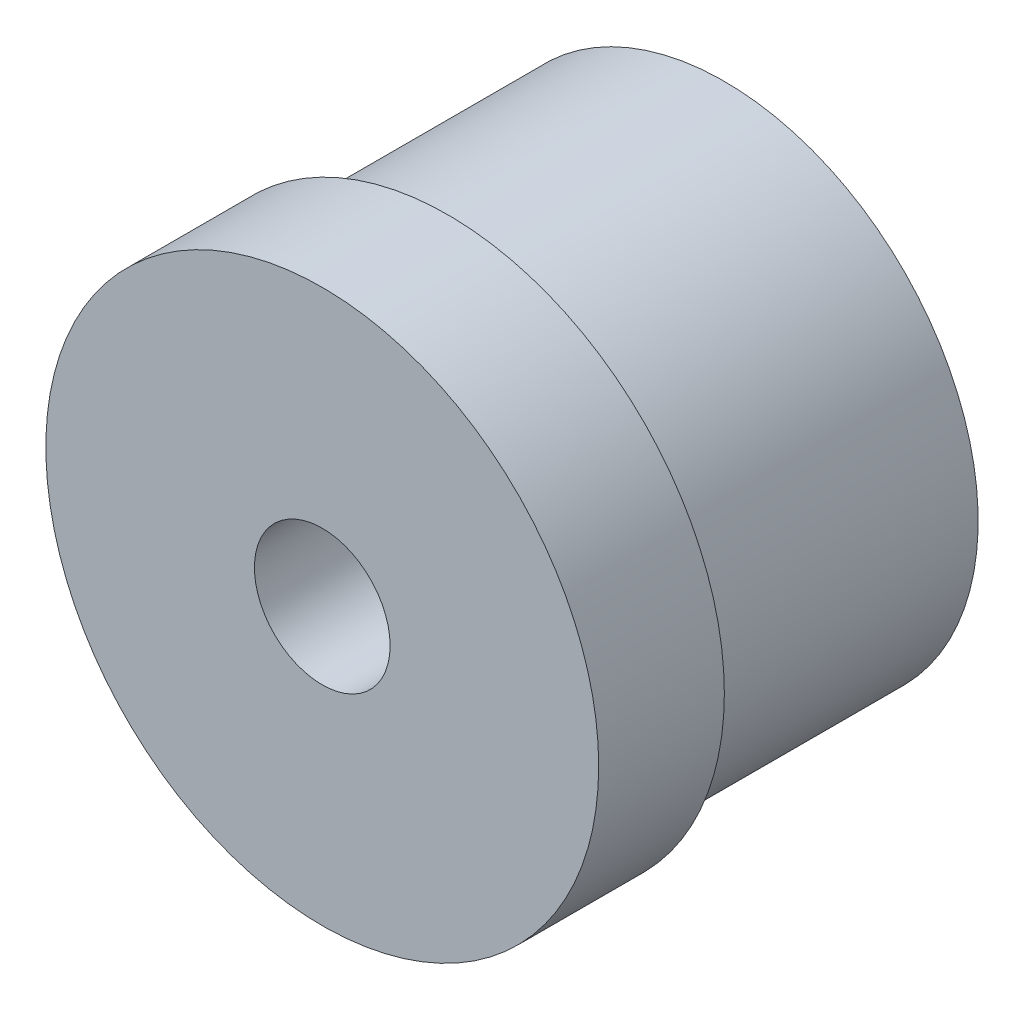
SolidWorks part; units mm, degrees
ref_plane "Front Plane" through (0, 0, 0) normal (0, 0, 1) x (1, 0, 0)
ref_plane "Top Plane" through (0, 0, 0) normal (0, 1, 0) x (1, 0, 0)
ref_plane "Right Plane" through (0, 0, 0) normal (1, 0, 0) x (0, 0, -1)
sketch "Sketch3" plane through (0, 0, 0) normal (0, 0, 1) x (1, 0, 0)
  circle A0 centre (0, 0) radius 11
  dimension "D1" = 22
extrude "Boss-Extrude1" add sketch "Sketch3" along normal blind 5
sketch "Sketch4" plane through (0, 0, 0) normal (0, 0, -1) x (-1, 0, 0)
  circle A0 centre (0, 0) radius 10.1
  dimension "D1" = 20.2
extrude "Boss-Extrude2" add sketch "Sketch4" along normal blind 11
sketch "Sketch5" plane through (0, 0, 5) normal (0, 0, 1) x (1, 0, 0)
  circle A0 centre (0, 0) radius 2.7
  dimension "D1" = 5.4
extrude "Cut-Extrude1" cut sketch "Sketch5" against normal through all
